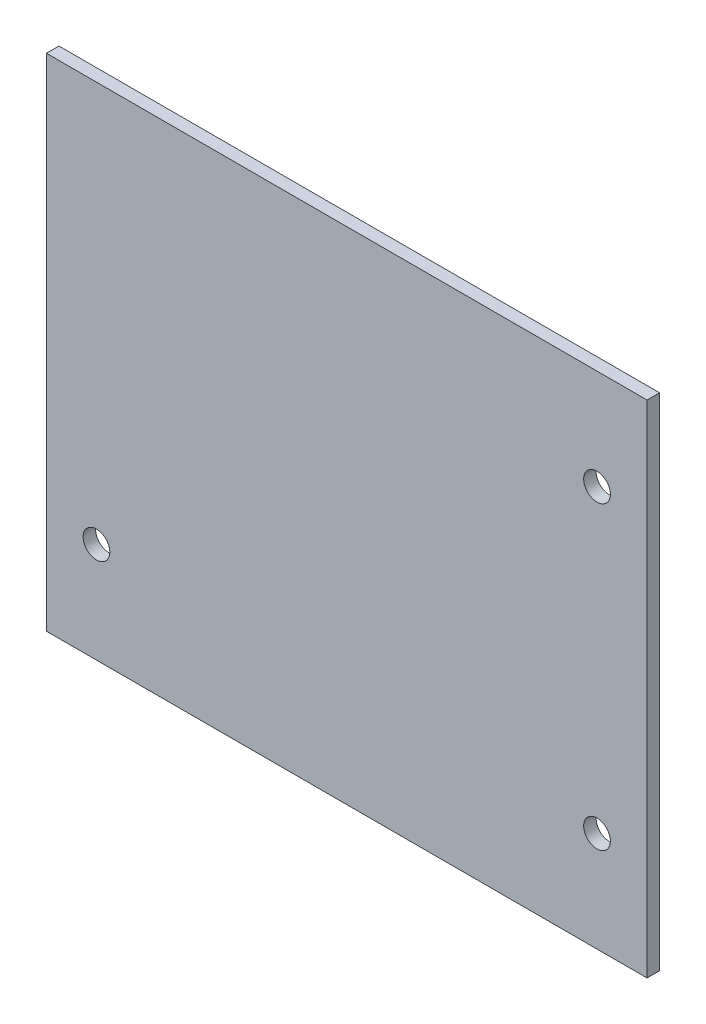
SolidWorks part; units mm, degrees
ref_plane "Front Plane" through (0, 0, 0) normal (0, 0, 1) x (1, 0, 0)
ref_plane "Top Plane" through (0, 0, 0) normal (0, 1, 0) x (1, 0, 0)
ref_plane "Right Plane" through (0, 0, 0) normal (1, 0, 0) x (0, 0, -1)
sketch "Sketch1" plane through (0, 0, 0) normal (0, 0, 1) x (1, 0, 0)
  line L1 (-76.2, -63.5) -> (76.2, -63.5)
  line L2 (-76.2, -63.5) -> (-76.2, 63.5)
  line L3 (-76.2, 63.5) -> (76.2, 63.5)
  line L4 (76.2, -63.5) -> (76.2, 63.5)
  line L5 (-76.2, -63.5) -> (76.2, 63.5) construction
  line L6 (-76.2, 63.5) -> (76.2, -63.5) construction
  circle A0 centre (63.5, 38.1) radius 3.3909
  circle A1 centre (63.5, -38.1) radius 3.3909
  circle A2 centre (-63.5, -38.1) radius 3.3909
  point P0 (0, 0)
  point P12 (0, 0)
  point P13 (0, 0)
  point P14 (0, 0)
  point P15 (-2.5775, -75.7797)
  point P16 (0, 0)
  dimension "D3" = 25.4
  dimension "D5" = 6.7818
  dimension "D1" = 127
  dimension "D2" = 152.4
  dimension "D4" = 12.7
  dimension "D6" = 12.7
  dimension "D7" = 101.6
extrude "Boss-Extrude1" add sketch "Sketch1" along normal blind 3.175
